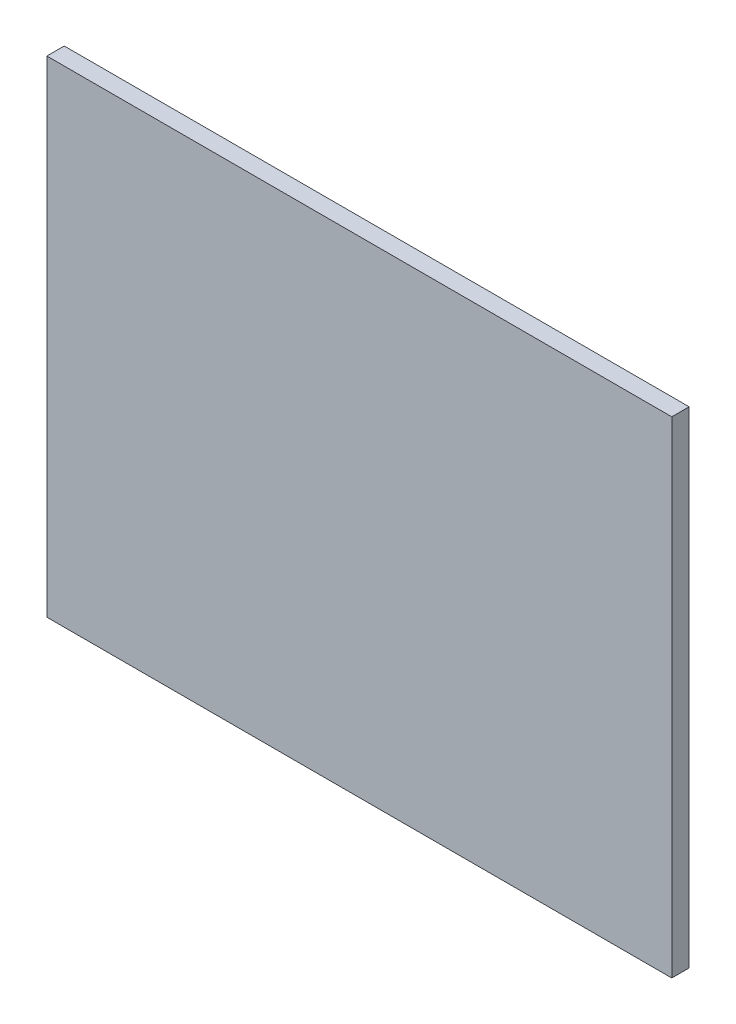
SolidWorks part; units mm, degrees
ref_plane "Front Plane" through (0, 0, 0) normal (0, 0, 1) x (1, 0, 0)
ref_plane "Top Plane" through (0, 0, 0) normal (0, 1, 0) x (1, 0, 0)
ref_plane "Right Plane" through (0, 0, 0) normal (1, 0, 0) x (0, 0, -1)
sketch "Sketch1" plane through (0, 0, 0) normal (0, 0, 1) x (1, 0, 0)
  line L1 (-90, 70) -> (90, 70)
  line L2 (-90, 70) -> (-90, -70)
  line L3 (-90, -70) -> (90, -70)
  line L4 (90, 70) -> (90, -70)
  dimension "D1" = 180
  dimension "D2" = 140
  dimension "D3" = 70
  dimension "D4" = 90
extrude "Boss-Extrude1" add sketch "Sketch1" along normal blind 5
